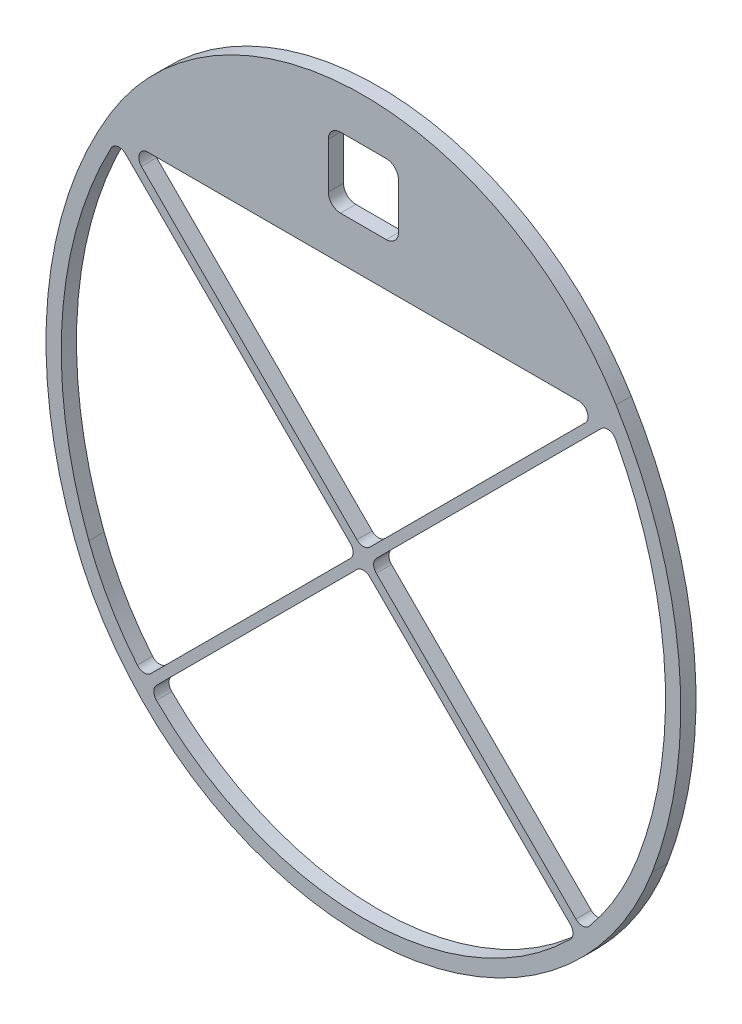
SolidWorks part; units mm, degrees
material "Balsa"
ref_plane "Front Plane" through (0, 0, 0) normal (0, 0, 1) x (1, 0, 0)
ref_plane "Top Plane" through (0, 0, 0) normal (0, 1, 0) x (1, 0, 0)
ref_plane "Right Plane" through (0, 0, 0) normal (1, 0, 0) x (0, 0, -1)
sketch "Sketch1" plane through (0, 0, 0) normal (0, 0, 1) x (1, 0, 0)
  line L8 (-114.3, 0) -> (114.3, 0) construction
  line L9 (-105.2065, 158.75) -> (105.2065, 158.75)
  line L10 (-101.6, 152.4) -> (101.6, 152.4)
  line L21 (-120.2398, -2.2453) -> (-114.3, 0)
  line L22 (114.3, 0) -> (120.2398, -2.2453)
  arc A0 (101.6, 152.4) -> (114.3, 0) centre (-52.0137, 62.8697) cw
  arc A1 (-101.6, 152.4) -> (-114.3, 0) centre (52.0137, 62.8697) ccw
  arc A2 (-105.2065, 158.75) -> (-120.2398, -2.2453) centre (52.0137, 62.8697) ccw
  arc A3 (105.2065, 158.75) -> (120.2398, -2.2453) centre (-52.0137, 62.8697) cw
  arc A4 (-107.0862, 155.5975) -> (-120.2398, -2.2453) centre (52.0137, 62.8697) ccw construction
  arc A5 (107.0862, 155.5975) -> (120.2398, -2.2453) centre (-52.0137, 62.8697) cw construction
  arc A6 (101.6, 152.4) -> (114.3, 0) centre (-52.0137, 62.8697) cw construction
  arc A7 (-101.6, 152.4) -> (-114.3, 0) centre (52.0137, 62.8697) ccw construction
  arc A8 (-105.2065, 158.75) -> (105.2065, 158.75) centre (0, 94.5901) cw
  arc A9 (-114.3, 0) -> (114.3, 0) centre (0, 43.2075) ccw
  arc A10 (-120.2398, -2.2453) -> (120.2398, -2.2453) centre (0, 43.2075) ccw
  point P0 (0, 0)
  point P13 (0, 152.4)
  dimension "D7" = 228.6
  dimension "D2" = 177.8
  dimension "D3" = 152.4
  dimension "D6" = 203.2
  dimension "D1" = 6.35
  dimension "D4" = 6.35
  dimension "D5" = 6.35
extrude "Boss-Extrude1" add sketch "Sketch1" along normal blind 6.35
sketch "Sketch2" plane through (0, 0, 6.35) normal (0, 0, 1) x (1, 0, 0)
  line L0 (0, 152.4) -> (0, 217.8171) construction
  line L1 (-14.605, 199.7136) -> (14.605, 199.7136)
  line L2 (-14.605, 199.7136) -> (-14.605, 170.5036)
  line L3 (-14.605, 170.5036) -> (14.605, 170.5036)
  line L4 (14.605, 199.7136) -> (14.605, 170.5036)
  line L5 (-14.605, 199.7136) -> (14.605, 170.5036) construction
  line L6 (-14.605, 170.5036) -> (14.605, 199.7136) construction
  line L7 (-101.6, 152.4) -> (101.6, 152.4) construction
  arc A0 (105.2065, 158.75) -> (-105.2065, 158.75) centre (0, 94.5901) ccw construction
  point P0 (0, 185.1086)
  point P15 (0, 185.1086)
  dimension "D1" = 29.21
  dimension "D2" = 29.21
extrude "Cut-Extrude1" cut sketch "Sketch2" against normal up to next
fillet "Fillet1" radius 5.08 4 edges at (14.605, 170.5036, 3.175) (14.605, 199.7136, 3.175) (-14.605, 199.7136, 3.175) (-14.605, 170.5036, 3.175)
sketch "Sketch3" plane through (0, 0, 6.35) normal (0, 0, 1) x (1, 0, 0)
  line L0 (-102.947, 151.053) -> (91.0265, -42.9206)
  line L3 (-102.947, 151.053) -> (-100.253, 153.747)
  line L4 (91.0265, -42.9206) -> (93.7206, -40.2265)
  line L5 (-100.253, 153.747) -> (93.7206, -40.2265)
  line L6 (-101.6, 152.4) -> (101.6, 152.4) construction
  line L7 (100.253, 153.747) -> (-93.7206, -40.2265)
  line L8 (100.253, 153.747) -> (102.947, 151.053)
  line L9 (-93.7206, -40.2265) -> (-91.0265, -42.9206)
  line L10 (102.947, 151.053) -> (-91.0265, -42.9206)
  point P0 (-101.6, 152.4)
  point P4 (101.6, 152.4)
  arc M11 (114.3, 0) -> (-114.3, 0) centre (0, 43.2075) cw
  arc M12 (-114.3, 0) -> (-101.6, 152.4) centre (52.0137, 62.8697) cw
  line M13 (-101.6, 152.4) -> (101.6, 152.4)
  arc M14 (101.6, 152.4) -> (114.3, 0) centre (-52.0137, 62.8697) cw
  dimension "D1" = 3.81
  dimension "D2" = 274.32
  dimension "D3" = 45
  dimension "D4" = 3.81
  dimension "45" = 45
  dimension "D6" = 274.32
extrude "Boss-Extrude2" add sketch "Sketch3" against normal up to surface (6.35 mm away) contours L10 L7 L5 M14 M13 | L5 L10 L0 M11 | L7 L5 L0 M13 M12 | L10 L5 L7 L0 up to face at (0, 185.1086, 0)
fillet "Fillet2" radius 3.81 12 edges at (-88.8187, -40.7128, 3.175) (88.8187, -40.7128, 3.175) (-91.3943, -37.9002, 3.175) (91.3943, -37.9002, 3.175) (-2.6941, 50.8, 3.175) (0, 48.1059, 3.175) (0, 53.4941, 3.175) (2.6941, 50.8, 3.175) (102.584, 150.6899, 3.175) (98.9059, 152.4, 3.175) (-102.584, 150.6899, 3.175) (-98.9059, 152.4, 3.175)
